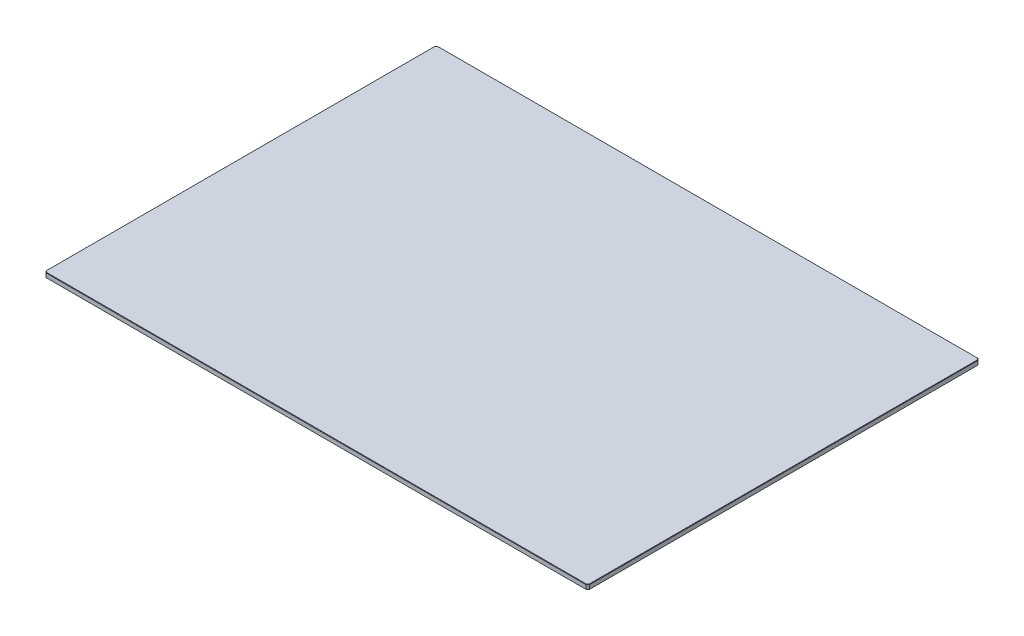
SolidWorks part; units mm, degrees
material "Glass"
ref_plane "Front Plane" through (0, 0, 0) normal (0, 0, 1) x (1, 0, 0)
ref_plane "Top Plane" through (0, 0, 0) normal (0, 1, 0) x (1, 0, 0)
ref_plane "Right Plane" through (0, 0, 0) normal (1, 0, 0) x (0, 0, -1)
sketch "Sketch1" plane through (0, 0, 0) normal (0, 1, 0) x (1, 0, 0)
  line L0 (0, 257.6125) -> (1.15, 258.7625)
  line L1 (0, 0) -> (358.775, 0) construction
  line L2 (0, 0) -> (0, 258.7625) construction
  line L3 (0, 258.7625) -> (358.775, 258.7625) construction
  line L4 (358.775, 0) -> (358.775, 258.7625) construction
  line L5 (179.3875, 258.7625) -> (179.3875, 0) construction
  line L6 (0, 129.3812) -> (358.775, 129.3812) construction
  line L7 (358.775, 257.6125) -> (357.625, 258.7625)
  line L8 (0, 1.15) -> (1.15, 0)
  line L9 (358.775, 1.15) -> (357.625, 0)
  line L10 (0, 1.15) -> (0, 257.6125)
  line L11 (1.15, 258.7625) -> (357.625, 258.7625)
  line L12 (358.775, 257.6125) -> (358.775, 1.15)
  line L13 (357.625, 0) -> (1.15, 0)
  dimension "D1" = 358.775
  dimension "D2" = 258.7625
  dimension "D3" = 2.3
  dimension "D4" = 2.3
extrude "Boss-Extrude1" add sketch "Sketch1" along normal blind 3.2
chamfer "Chamfer1" distance 0.254 angle 45 16 edges at (0.575, 0, -0.575) (179.3875, 0, 0) (358.2, 0, -0.575) (358.775, 0, -129.3812) (358.2, 0, -258.1875) (179.3875, 0, -258.7625) (0.575, 0, -258.1875) (0, 0, -129.3812) (0.575, 3.2, -258.1875) (179.3875, 3.2, -258.7625) (358.2, 3.2, -258.1875) (358.775, 3.2, -129.3812) (358.2, 3.2, -0.575) (179.3875, 3.2, 0) (0.575, 3.2, -0.575) (0, 3.2, -129.3812)
equation "\"glass pane length\" = 14.125"
equation "\"glass pane width\" = 10.1875"
equation "\"D1@Sketch1\"=\"glass pane length\""
equation "\"D2@Sketch1\"=\"glass pane width\""
